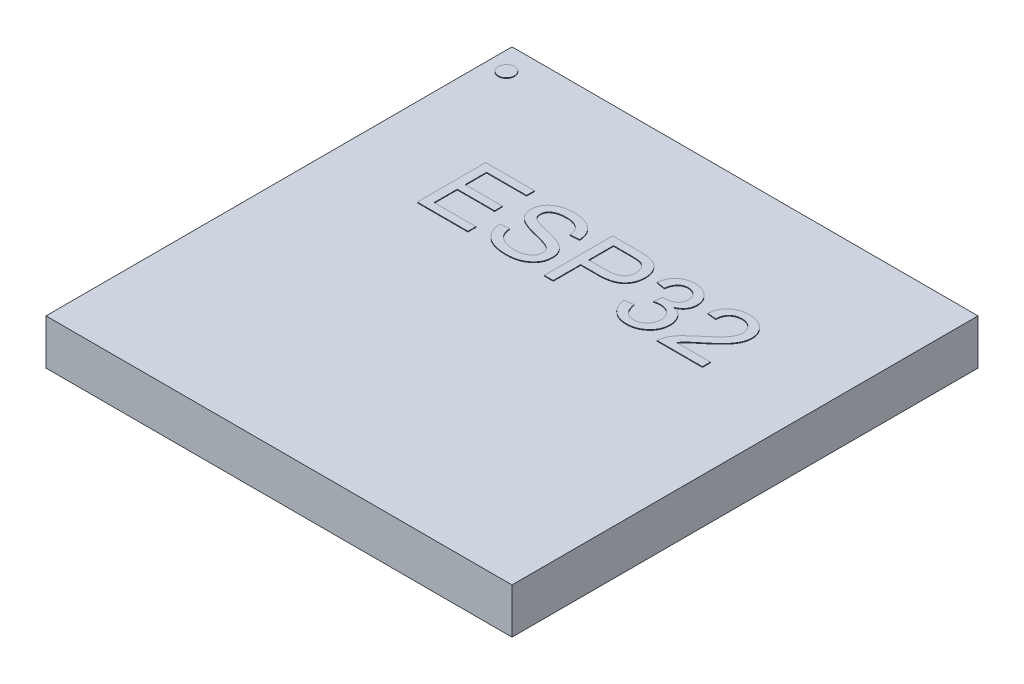
SolidWorks part; units mm, degrees
material "Plastique personnalisé"
ref_plane "Plan de face" through (0, 0, 0) normal (0, 0, 1) x (1, 0, 0)
ref_plane "Plan de dessus" through (0, 0, 0) normal (0, 1, 0) x (1, 0, 0)
ref_plane "Plan de droite" through (0, 0, 0) normal (1, 0, 0) x (0, 0, -1)
sketch "Esquisse1" plane through (0, 0, 0) normal (0, 1, 0) x (1, 0, 0)
  line L1 (0, 0) -> (7, 0)
  line L2 (0, 0) -> (0, 7)
  line L3 (0, 7) -> (7, 7)
  line L4 (7, 0) -> (7, 7)
  dimension "D1" = 7
  dimension "D2" = 7
extrude "Boss.-Extru.1" add sketch "Esquisse1" along normal blind 0.68
sketch "Esquisse2" plane through (0, 0.68, 0) normal (0, 1, 0) x (1, 0, 0)
  text T0 "ESP32" font "@Arial Unicode MS" height in points 4
extrude "Boss.-Extru.2" add sketch "Esquisse2" along normal blind 0.01
sketch "Esquisse3" plane through (0, 0.68, 0) normal (0, 1, 0) x (1, 0, 0)
  circle A0 centre (0.2844, 6.6315) radius 0.1212
extrude "Boss.-Extru.3" add sketch "Esquisse3" along normal blind 0.01
